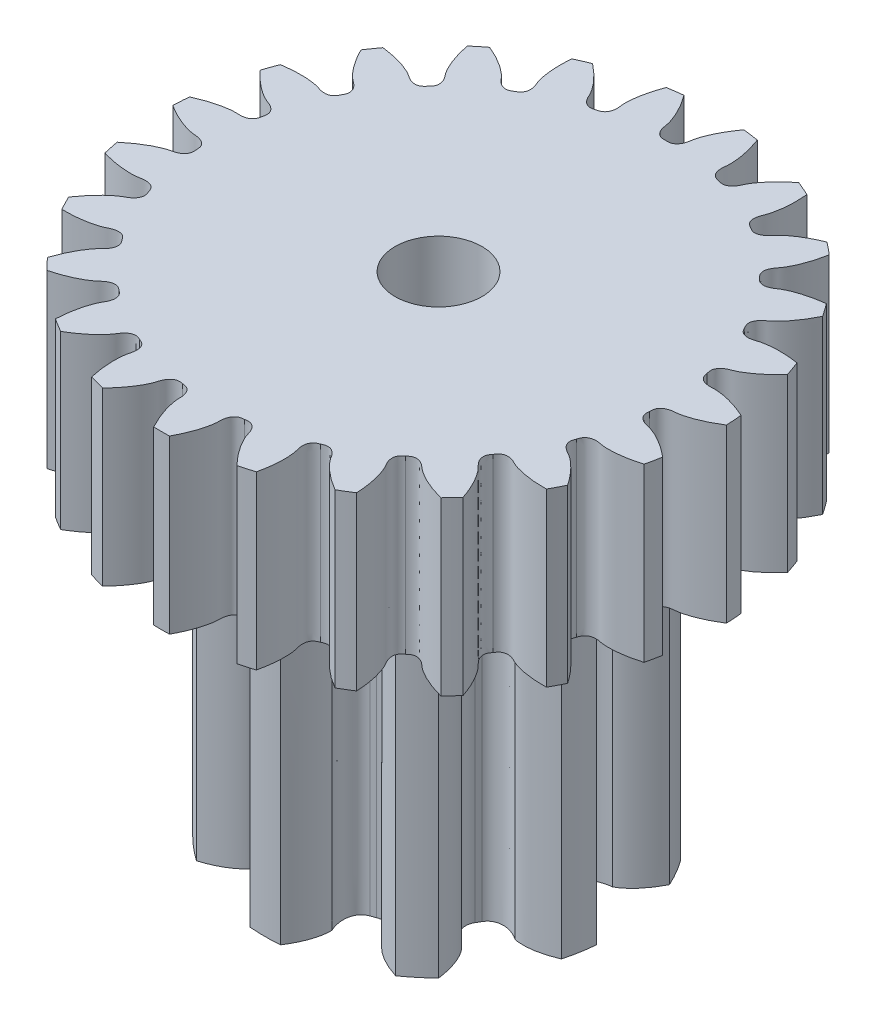
SolidWorks part; units mm, degrees
ref_plane "Front Plane" through (0, 0, 0) normal (0, 0, 1) x (1, 0, 0)
ref_plane "Top Plane" through (0, 0, 0) normal (0, 1, 0) x (1, 0, 0)
ref_plane "Right Plane" through (0, 0, 0) normal (1, 0, 0) x (0, 0, -1)
sketch "Sketch1" plane through (0, 0, 0) normal (0, 0, 1) x (1, 0, 0)
  line L0 (-6.375, 11.25) -> (-6.375, 7.3)
  line L1 (-6.375, 7.3) -> (-4, 7.3)
  line L2 (-4, 7.3) -> (-4, 0)
  line L3 (-4, 0) -> (0, 0)
  line L4 (-6.375, 11.25) -> (0, 11.25)
  line L5 (0, 11.25) -> (0, 0) construction
  line L6 (0, 0) -> (0, 11.25)
  dimension "D1" = 6.375
  dimension "D2" = 3.95
  dimension "D3" = 11.25
  dimension "D4" = 4
revolve "Revolve1" add sketch "Sketch1" angle 360 about L5
sketch "Sketch2" plane through (0, 11.25, 0) normal (0, 1, 0) x (1, 0, 0)
  circle A0 centre (0, 0) radius 0.8
  dimension "D1" = 1.6
extrude "Cut-Extrude1" [suppressed] cut sketch "Sketch2" against normal through all
sketch "Sketch9" plane through (0, 11.25, 0) normal (0, 1, 0) x (1, 0, 0)
  circle A0 centre (0, 0) radius 1
  dimension "D1" = 2
extrude "Cut-Extrude8" cut sketch "Sketch9" against normal through all
ref_axis "Axis1" [suppressed] through (0, 0, 0) along (0, 1, 0)
sketch "Sketch6" plane through (0, 0, 0) normal (0, 1, 0) x (1, 0, 0)
  line L0 (0, 0) -> (0, 8.2669) construction
  arc A0 (-0.7527, 6.4225) -> (0.7527, 6.4225) centre (0, 0) cw
  spline S0 degree 3 poles (-0.7527, 6.4225) (-0.6995, 6.3549) (-0.6261, 6.2541) (-0.5404, 6.1191) (-0.4872, 6.0272) (-0.4421, 5.9414) (-0.4045, 5.8622) (-0.3738, 5.7901) (-0.3493, 5.7253) (-0.3304, 5.6684) (-0.3163, 5.6196) (-0.3065, 5.5793) (-0.3, 5.5476) (-0.2965, 5.525) (-0.2942, 5.5079) (-0.2919, 5.4937) (-0.2883, 5.4745) (-0.2822, 5.4468) (-0.2719, 5.4113) (-0.257, 5.3731) (-0.2378, 5.3364) (-0.2124, 5.3009) (-0.1778, 5.2674) (-0.1098, 5.2263) (-0.0435, 5.2242) (0, 5.2272) knots 0 0 0 0 0.173174 0.250484 0.321609 0.386549 0.445305 0.497875 0.544261 0.584463 0.618479 0.64631 0.667957 0.683419 0.692448 0.702521 0.71241 0.731687 0.759574 0.786733 0.813985 0.842551 0.874112 0.910406 1 1 1 1
  spline S1 degree 3 poles (0.7527, 6.4225) (0.6995, 6.3549) (0.6261, 6.2541) (0.5404, 6.1191) (0.4872, 6.0272) (0.4421, 5.9414) (0.4045, 5.8622) (0.3738, 5.7901) (0.3493, 5.7253) (0.3304, 5.6684) (0.3163, 5.6196) (0.3065, 5.5793) (0.3, 5.5476) (0.2965, 5.525) (0.2942, 5.5079) (0.2919, 5.4937) (0.2883, 5.4745) (0.2822, 5.4468) (0.2719, 5.4113) (0.257, 5.3731) (0.2378, 5.3364) (0.2124, 5.3009) (0.1778, 5.2674) (0.1098, 5.2263) (0.0435, 5.2242) (0, 5.2272) knots 0 0 0 0 0.173174 0.250484 0.321609 0.386549 0.445305 0.497875 0.544261 0.584463 0.618479 0.64631 0.667957 0.683419 0.692448 0.702521 0.71241 0.731687 0.759574 0.786733 0.813985 0.842551 0.874112 0.910406 1 1 1 1
extrude "Cut-Extrude5" cut sketch "Sketch6" along normal through all
pattern_circular "CirPattern3" count 23 over 360 about axis through (0, 0, 0) along (0, 1, 0) of "Cut-Extrude5"
sketch "Sketch8" plane through (0, 0, 0) normal (0, 1, 0) x (1, 0, 0)
  line L0 (0, 0) -> (0, 4.722) construction
  arc A0 (-1.1311, 3.9343) -> (1.1311, 3.9343) centre (0, 0) cw
  arc A1 (-0.0605, 2.5118) -> (0.0605, 2.5118) centre (0, 0) cw
  spline S0 degree 3 poles (-0.4508, 3.1371) (-0.4555, 3.1552) (-0.4662, 3.1866) (-0.4857, 3.2336) (-0.5088, 3.2815) (-0.5392, 3.3365) (-0.5777, 3.398) (-0.6251, 3.4651) (-0.6822, 3.5372) (-0.7496, 3.6131) (-0.8279, 3.6922) (-0.9523, 3.8046) (-1.0565, 3.8836) (-1.1311, 3.9343) knots 0 0 0 0 0.052408 0.093213 0.143086 0.202027 0.270036 0.347113 0.433258 0.528471 0.632751 0.7461 1 1 1 1
  spline S1 degree 3 poles (0.4508, 3.1371) (0.4555, 3.1552) (0.4662, 3.1866) (0.4857, 3.2336) (0.5088, 3.2815) (0.5392, 3.3365) (0.5777, 3.398) (0.6251, 3.4651) (0.6822, 3.5372) (0.7496, 3.6131) (0.8279, 3.6922) (0.9523, 3.8046) (1.0565, 3.8836) (1.1311, 3.9343) knots 0 0 0 0 0.052408 0.093213 0.143086 0.202027 0.270036 0.347113 0.433258 0.528471 0.632751 0.7461 1 1 1 1
  spline S2 degree 3 poles (-0.4508, 3.1371) (-0.454, 3.0847) (-0.4536, 3.0214) (-0.4434, 2.9285) (-0.4309, 2.8597) (-0.4049, 2.7764) (-0.3685, 2.6999) (-0.32, 2.6308) (-0.2566, 2.5714) (-0.1699, 2.5233) (-0.0997, 2.5117) (-0.0605, 2.5118) knots 0 0 0 0 0.190558 0.228772 0.338905 0.443507 0.544594 0.644963 0.74813 0.857409 1 1 1 1
  spline S3 degree 3 poles (0.4508, 3.1371) (0.454, 3.0847) (0.4536, 3.0214) (0.4434, 2.9285) (0.4309, 2.8597) (0.4049, 2.7764) (0.3685, 2.6999) (0.32, 2.6308) (0.2566, 2.5714) (0.1699, 2.5233) (0.0997, 2.5117) (0.0605, 2.5118) knots 0 0 0 0 0.190558 0.228772 0.338905 0.443507 0.544594 0.644963 0.74813 0.857409 1 1 1 1
extrude "Cut-Extrude7" cut sketch "Sketch8" along normal up to surface (7.3 mm away) up to face at (-4, 7.3, 0)
pattern_circular "CirPattern5" count 9 over 360 about axis through (0, 0, 0) along (0, 1, 0) of "Cut-Extrude7"
sketch "Sketch for Gear Mate" plane through (0, 11.25, 0) normal (0, 1, 0) x (1, 0, 0)
  circle A0 centre (0, 0) radius 2.7766
